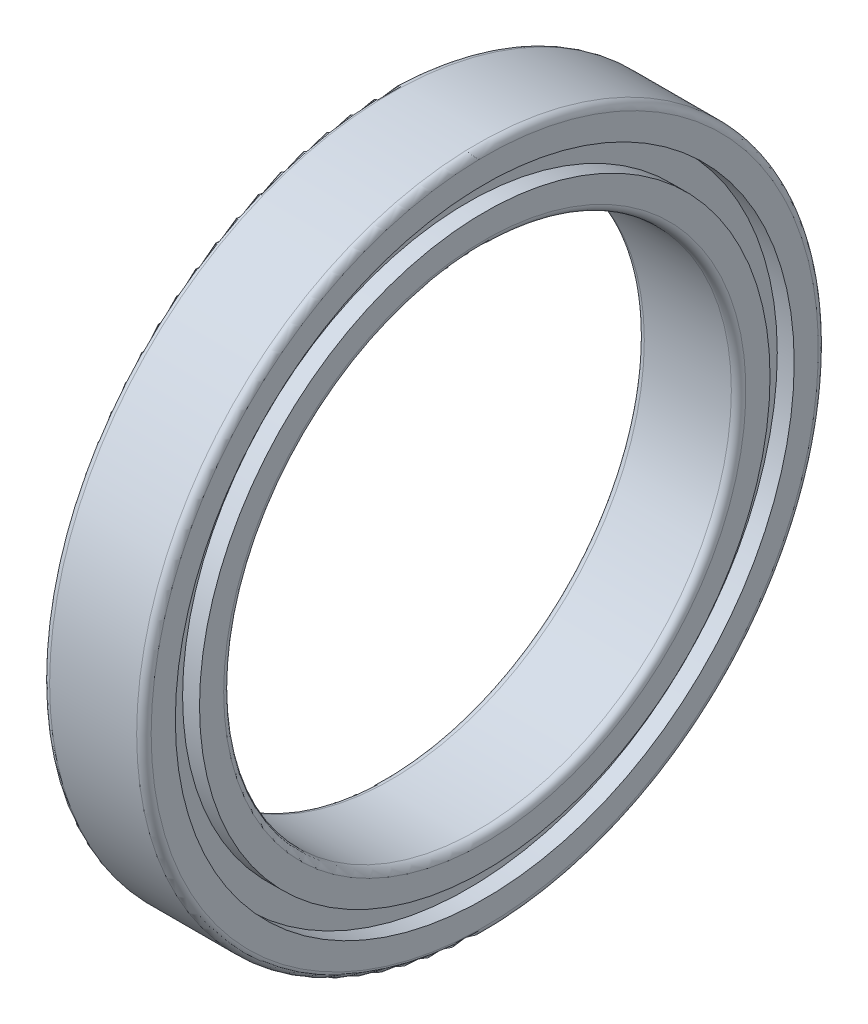
SolidWorks part; units mm, degrees
material "AISI 1020"
ref_plane "Спереди" through (0, 0, 0) normal (0, 0, 1) x (1, 0, 0)
ref_plane "Сверху" through (0, 0, 0) normal (0, 1, 0) x (1, 0, 0)
ref_plane "Справа" through (0, 0, 0) normal (1, 0, 0) x (0, 0, -1)
sketch "Эскиз1" plane through (0, 0, 0) normal (0, 0, 1) x (1, 0, 0)
  line L0 (-1000, 0) -> (49000, 0) construction
  line L1 (0, -1000) -> (0, 49000) construction
  line L2 (3, 17.5) -> (-3, 17.5)
  line L3 (-3.5, 18) -> (-3.5, 19.6667)
  line L4 (-3.5, 19.6667) -> (-2.3333, 19.6667)
  line L5 (-2.3333, 19.6667) -> (-2.3333, 21.3333)
  line L6 (-2.3333, 21.3333) -> (-3.5, 21.3333)
  line L7 (-3.5, 21.3333) -> (-3.5, 23)
  line L8 (-3, 23.5) -> (3, 23.5)
  line L9 (3.5, 21.3333) -> (3.5, 23)
  line L10 (2.3333, 21.3333) -> (3.5, 21.3333)
  line L11 (2.3333, 19.6667) -> (2.3333, 21.3333)
  line L12 (3.5, 19.6667) -> (2.3333, 19.6667)
  line L13 (3.5, 18) -> (3.5, 19.6667)
  arc A0 (-3, 17.5) -> (-3.5, 18) centre (-3, 18) cw
  arc A1 (-3.5, 23) -> (-3, 23.5) centre (-3, 23) cw
  arc A2 (3.5, 23) -> (3, 23.5) centre (3, 23) ccw
  arc A3 (3, 17.5) -> (3.5, 18) centre (3, 18) ccw
  point P23 (0, 23.5)
  point P27 (0, 17.5)
  dimension "_r" = 0.5
  dimension "_d" = 35
  dimension "D" = 47
  dimension "B" = 7
  dimension "D2" = 4.6667
revolve "Повернуть1" add sketch "Эскиз1" angle 360 about L0
equation "\"D2@Эскиз1\"= \"B@Эскиз1\" / 3 * 2"
